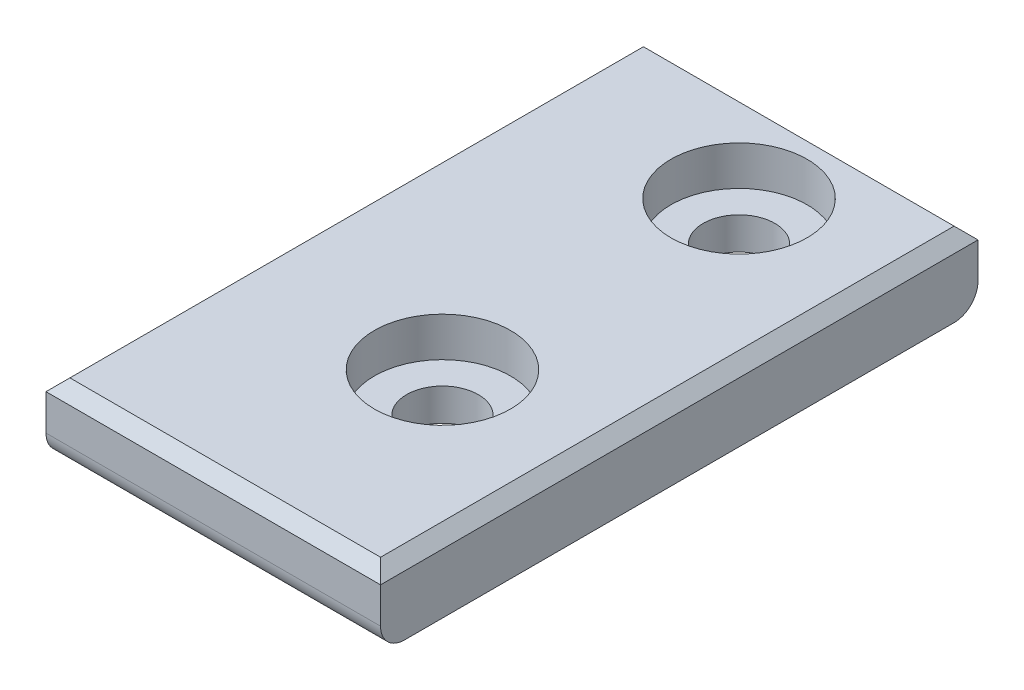
SolidWorks part; units mm, degrees
ref_plane "Front Plane" through (0, 0, 0) normal (0, 0, 1) x (1, 0, 0)
ref_plane "Top Plane" through (0, 0, 0) normal (0, 1, 0) x (1, 0, 0)
ref_plane "Right Plane" through (0, 0, 0) normal (1, 0, 0) x (0, 0, -1)
sketch "Sketch1" plane through (0, 0, 0) normal (0, 1, 0) x (1, 0, 0)
  line L1 (0, 0) -> (14, 0)
  line L2 (0, 0) -> (0, 25)
  line L3 (0, 25) -> (14, 25)
  line L4 (14, 0) -> (14, 25)
  circle A0 centre (8, 21) radius 1.5
  circle A1 centre (8, 8.5895) radius 1.5
  dimension "D6" = 3
  dimension "D1" = 14
  dimension "D2" = 25
  dimension "D3" = 4
  dimension "D4" = 6
  dimension "D5" = 16.4105
extrude "Boss-Extrude1" add sketch "Sketch1" along normal blind 3
chamfer "Chamfer1" distance 0.5 angle 45 4 edges at (7, 3, -25) (0, 3, -12.5) (7, 3, 0) (14, 3, -12.5)
fillet "Fillet1" radius 1 2 edges at (7, 0, 0) (7, 0, -25)
sketch "Sketch2" plane through (0, 3, 0) normal (0, 1, 0) x (1, 0, 0)
  circle A0 centre (8, 21) radius 2.85
  circle A1 centre (8, 8.5895) radius 2.85
  dimension "D1" = 5.7
extrude "Cut-Extrude1" cut sketch "Sketch2" against normal blind 1.65
sketch "Sketch3" plane through (0, 0, 0) normal (0, -1, 0) x (1, 0, 0)
  line L0 (14, -25) -> (0, -25) construction
  line L1 (5.5, -25) -> (10.5, -25)
  line L2 (4.5, -24) -> (4.5, -23)
  line L3 (4.5, -23) -> (11.5, -23)
  line L4 (11.5, -24) -> (11.5, -23)
  line L6 (14, -25) -> (14, -24) construction
  arc A0 (4.5, -24) -> (5.5, -25) centre (5.5, -24) ccw
  arc A1 (10.5, -25) -> (11.5, -24) centre (10.5, -24) ccw
  point P11 (4.5, -25)
  point P14 (11.5, -25)
  dimension "D4" = 1
  dimension "D1" = 2.5
  dimension "D2" = 7
  dimension "D3" = 2
extrude "Boss-Extrude2" add sketch "Sketch3" against normal up to vertex
